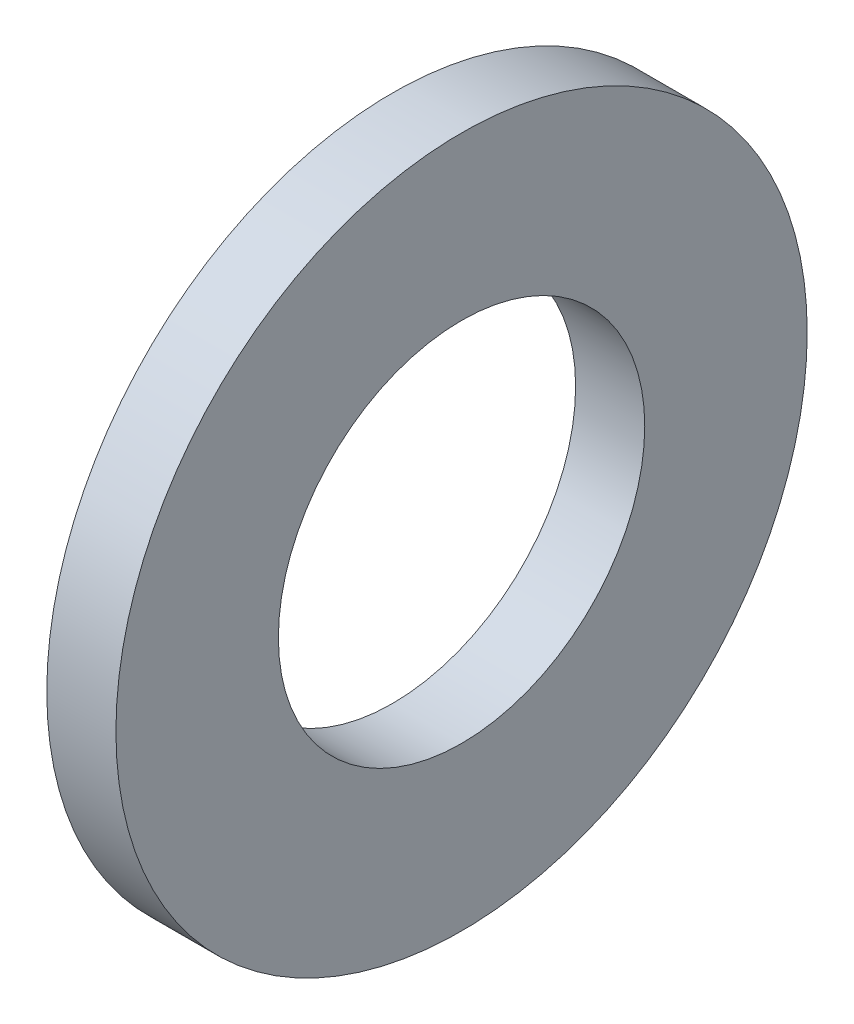
SolidWorks part; units mm, degrees
ref_plane "Plane1" through (0, 0, 0) normal (0, 0, 1) x (1, 0, 0)
ref_plane "Plane2" through (0, 0, 0) normal (0, 1, 0) x (1, 0, 0)
ref_plane "Plane3" through (0, 0, 0) normal (1, 0, 0) x (0, 0, -1)
sketch "Sketch1" plane through (0, 0, 0) normal (0, 0, 1) x (1, 0, 0)
  line L0 (-34.925, 0) -> (9.525, 0) construction
  line L1 (0, 2.65) -> (0, 5)
  line L2 (0, 5) -> (-1, 5)
  line L3 (-1, 5) -> (-1, 2.65)
  line L4 (-1, 2.65) -> (0, 2.65)
  dimension "Thickness" = 1
  dimension "Inside_dia" = 5.3
  dimension "Outside_dia" = 10
revolve "Base-Revolve" add sketch "Sketch1" angle 360 about L0
chamfer "ODChamfer" [suppressed] distance 0.25 angle 45
equation "\"D1@ODChamfer\" =  \"Thickness@Sketch1\" * 0.25"
